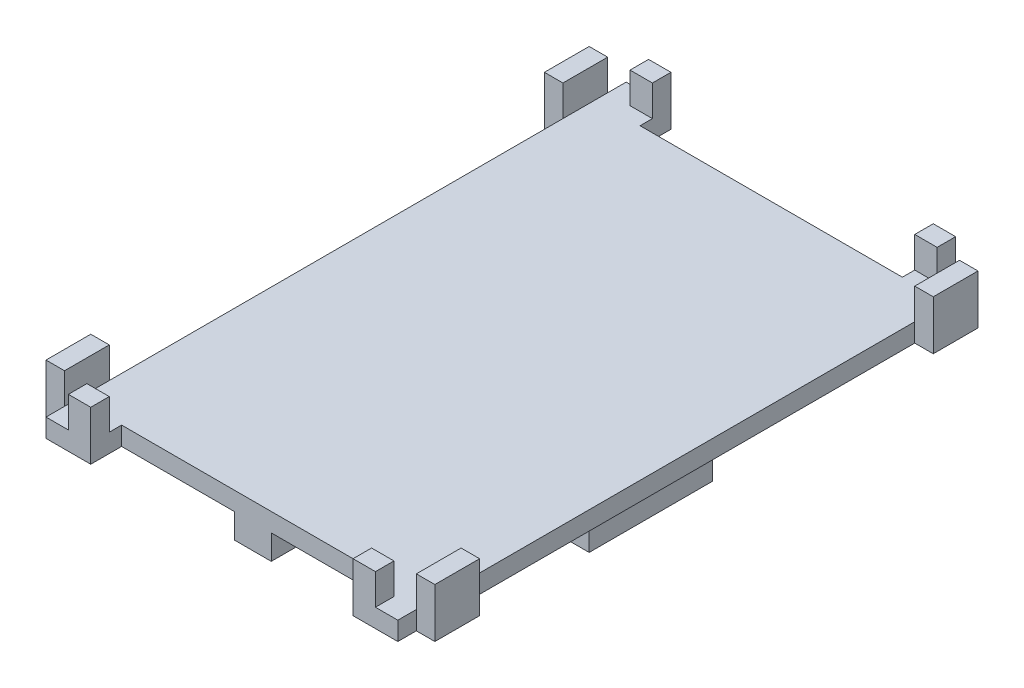
SolidWorks part; units mm, degrees
ref_plane "Płaszczyzna przednia" through (0, 0, 0) normal (0, 0, 1) x (1, 0, 0)
ref_plane "Płaszczyzna górna" through (0, 0, 0) normal (0, 1, 0) x (1, 0, 0)
ref_plane "Płaszczyzna prawa" through (0, 0, 0) normal (1, 0, 0) x (0, 0, -1)
sketch "Sketch2" plane through (0, 0, 0) normal (0, 0, 1) x (1, 0, 0)
  line L0 (0, 0) -> (17.5, 0) construction
  line L5 (0, 0) -> (-17.5, 0) construction
  line L7 (-17.5, 0) -> (-17.5, -1) construction
  line L8 (17.5, 0) -> (17.5, -1) construction
  line L9 (17.5, -1) -> (13.5, -1) construction
  line L10 (13.5, -1) -> (13.5, -7.5) construction
  line L11 (-17.5, -1) -> (-13.5, -1) construction
  line L12 (-13.5, -1) -> (-13.5, -7.5) construction
  line L13 (-13.5, -7.5) -> (13.5, -7.5) construction
  line L14 (-17.6, 0) -> (-17.6, -1.1) construction
  line L15 (-17.6, 0) -> (-17.6, -1.1)
  line L16 (-17.6, -1.1) -> (-14.5, -1.1)
  line L17 (-14.5, -1.1) -> (-14.5, -5)
  line L18 (-14.5, -5) -> (-22.5, -5)
  line L19 (-22.5, -5) -> (-22.5, 0)
  line L20 (-22.5, 0) -> (-22.5, 4)
  line L21 (-22.5, 4) -> (22.5, 4)
  line L22 (22.5, 4) -> (22.5, -5)
  line L23 (22.5, -5) -> (14.5, -5)
  line L24 (14.5, -5) -> (14.5, -1.1)
  line L25 (14.5, -1.1) -> (17.6, -1.1)
  line L26 (17.6, -1.1) -> (17.6, 0)
  line L27 (17.6, 0) -> (-17.6, 0)
  point P10 (-22.5, 0)
  point P11 (-22.5, -5)
  point P12 (-14.5, -5)
  point P13 (-22.5, 0)
  point P14 (-22.5, 4)
  point P16 (-14.5, -1.1)
  point P17 (-17.6, -1.1)
  point P18 (-17.6, 0)
  dimension "D1" = 5
  dimension "D2" = 5
  dimension "D3" = 8
  dimension "D4" = 4
  dimension "D5" = 0.1
  dimension "D6" = 0.1
  dimension "D7" = 35
  dimension "D8" = 1
  dimension "D9" = 4
  dimension "D10" = 4
  dimension "D11" = 1
  dimension "D12" = 27
  dimension "D13" = 6.5
  dimension "D14" = 6.5
  dimension "D16" = 3.1
  dimension "D17" = 1
  dimension "D18" = 9
  dimension "D19" = 9
  dimension "D20" = 8
  dimension "D21" = 1
  dimension "D22" = 0.1
  dimension "D23" = 0.1
  dimension "D25" = 45
extrude "Boss-Extrude1" add sketch "Sketch2" along normal blind 20
sketch "Sketch3" plane through (0, 4, 0) normal (0, 1, 0) x (1, 0, 0)
  line L0 (22.5, -20) -> (-22.5, -20) construction
  line L1 (-22.5, -20) -> (-22.5, 0) construction
  line L2 (-21.25, -52) -> (21.25, -52)
  line L3 (28.5, -46.75) -> (28.5, 26.75)
  line L4 (-28.5, -46.75) -> (-28.5, 26.75)
  line L5 (28.5, -54) -> (-28.5, 34) construction
  line L6 (-28.5, -54) -> (28.5, 34) construction
  line L7 (21.25, -54) -> (21.25, -52)
  line L8 (-21.25, -54) -> (-21.25, -52)
  line L9 (21.25, -54) -> (-21.25, 34) construction
  line L10 (-21.25, -54) -> (21.25, 34) construction
  line L11 (-21.25, 32) -> (21.25, 32)
  line L12 (21.25, 32) -> (21.25, 34)
  line L13 (-21.25, 32) -> (-21.25, 34)
  line L14 (21.25, -54) -> (21.25, -57)
  line L15 (28.5, -54) -> (28.5, -57)
  line L16 (21.25, -57) -> (28.5, -57)
  line L17 (28.5, -54) -> (31.5, -54)
  line L18 (31.5, -54) -> (31.5, -46.75)
  line L19 (28.5, -46.75) -> (31.5, -46.75)
  line L20 (-21.25, -54) -> (-21.25, -57)
  line L21 (-28.5, -54) -> (-28.5, -57)
  line L22 (-21.25, -57) -> (-28.5, -57)
  line L23 (-28.5, -54) -> (-31.5, -54)
  line L24 (-31.5, -54) -> (-31.5, -46.75)
  line L25 (-28.5, -46.75) -> (-31.5, -46.75)
  line L26 (-21.25, 34) -> (-21.25, 37)
  line L27 (-28.5, 34) -> (-28.5, 37)
  line L28 (-21.25, 37) -> (-28.5, 37)
  line L29 (-28.5, 34) -> (-31.5, 34)
  line L30 (-31.5, 34) -> (-31.5, 26.75)
  line L31 (-28.5, 26.75) -> (-31.5, 26.75)
  line L32 (21.25, 34) -> (21.25, 37)
  line L33 (28.5, 34) -> (28.5, 37)
  line L34 (21.25, 37) -> (28.5, 37)
  line L35 (28.5, 34) -> (31.5, 34)
  line L36 (31.5, 34) -> (31.5, 26.75)
  line L37 (28.5, 26.75) -> (31.5, 26.75)
  point P0 (0, -10)
  point P5 (0, -10)
  point P10 (0, -10)
  point P41 (-1.8729, 30.2425)
  dimension "D1" = 10
  dimension "D2" = 22.5
  dimension "D3" = 57
  dimension "D4" = 88
  dimension "D5" = 3
  dimension "D6" = 3
  dimension "D7" = 7.25
  dimension "D8" = 3
  dimension "D9" = 3
  dimension "D10" = 7.25
  dimension "D11" = 7.25
  dimension "D12" = 42
  dimension "D13" = 42
extrude "Boss-Extrude2" add sketch "Sketch3" along normal blind 3
sketch "Sketch4" plane through (0, 7, 0) normal (0, 1, 0) x (1, 0, 0)
  line L0 (31.5, 34) -> (28.5, 34) construction
  line L1 (-31.5, 34) -> (-28.5, 34)
  line L2 (-31.5, 34) -> (-31.5, 26.75)
  line L3 (-31.5, 26.75) -> (-28.5, 26.75)
  line L4 (-28.5, 34) -> (-28.5, 26.75)
  line L5 (28.5, 26.75) -> (31.5, 26.75)
  line L6 (28.5, 26.75) -> (28.5, 34)
  line L7 (28.5, 34) -> (31.5, 34)
  line L8 (31.5, 26.75) -> (31.5, 34)
  line L10 (28.5, -46.75) -> (31.5, -46.75)
  line L11 (28.5, -46.75) -> (28.5, -54)
  line L12 (28.5, -54) -> (31.5, -54)
  line L13 (31.5, -46.75) -> (31.5, -54)
  line L14 (-31.5, -46.75) -> (-28.5, -46.75)
  line L15 (-31.5, -46.75) -> (-31.5, -54)
  line L16 (-31.5, -54) -> (-28.5, -54)
  line L17 (-28.5, -46.75) -> (-28.5, -54)
extrude "Boss-Extrude3" add sketch "Sketch4" along normal blind 5
sketch "Sketch5" plane through (0, 7, 0) normal (0, 1, 0) x (1, 0, 0)
  line L1 (-21.25, 37) -> (-24.875, 37)
  line L2 (-21.25, 37) -> (-21.25, 34)
  line L3 (-21.25, 34) -> (-24.875, 34)
  line L4 (-24.875, 37) -> (-24.875, 34)
  line L5 (21.25, 37) -> (24.875, 37)
  line L6 (21.25, 37) -> (21.25, 34)
  line L7 (21.25, 34) -> (24.875, 34)
  line L8 (24.875, 37) -> (24.875, 34)
  line L9 (21.25, -57) -> (24.875, -57)
  line L10 (21.25, -57) -> (21.25, -54)
  line L11 (21.25, -54) -> (24.875, -54)
  line L12 (24.875, -57) -> (24.875, -54)
  line L13 (-21.25, -57) -> (-24.875, -57)
  line L14 (-21.25, -57) -> (-21.25, -54)
  line L15 (-21.25, -54) -> (-24.875, -54)
  line L16 (-24.875, -57) -> (-24.875, -54)
extrude "Boss-Extrude4" add sketch "Sketch5" along normal blind 5
sketch "Sketch6" plane through (0, 4, 0) normal (0, -1, 0) x (1, 0, 0)
  line L0 (-28.5, 54) -> (28.5, -34) construction
  line L1 (-3, -32) -> (3, -32)
  line L2 (-3, -32) -> (-3, 52)
  line L3 (-3, 52) -> (3, 52)
  line L4 (3, -32) -> (3, 52)
  line L5 (-3, -32) -> (3, 52) construction
  line L6 (-3, 52) -> (3, -32) construction
  line L7 (-21.25, 52) -> (21.25, 52) construction
  point P0 (0, 10)
  dimension "D1" = 6
extrude "Boss-Extrude5" add sketch "Sketch6" along normal blind 4
